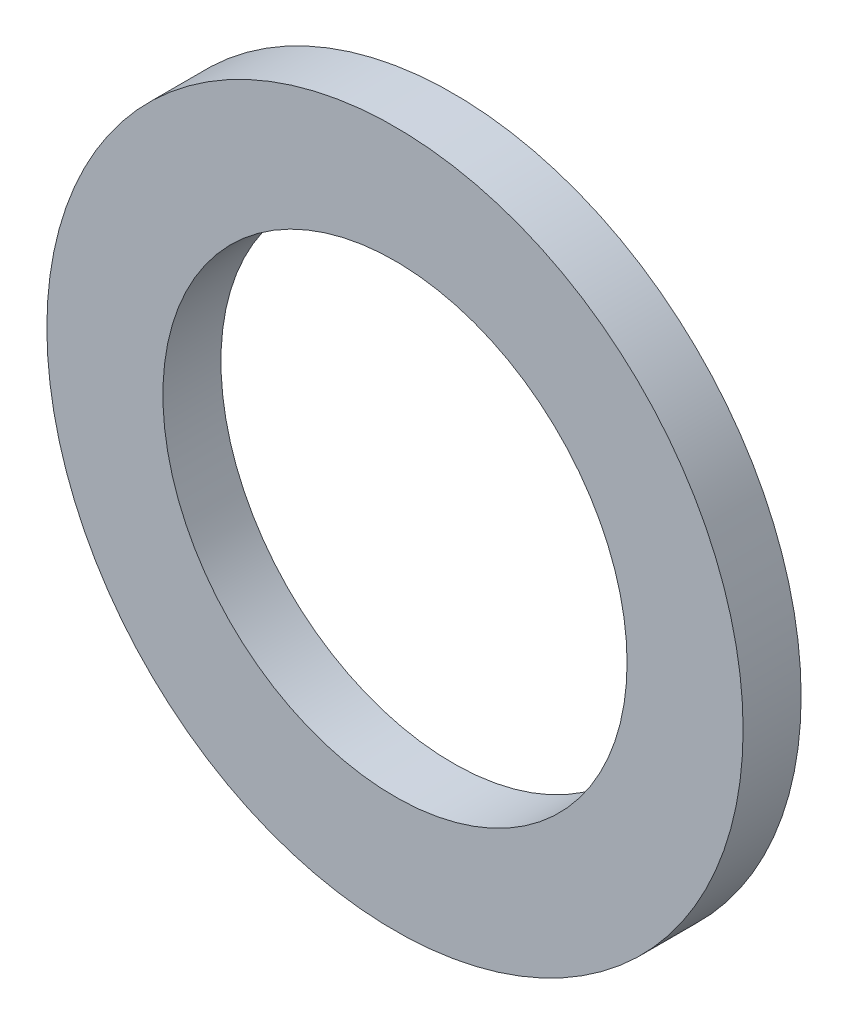
SolidWorks part; units mm, degrees
ref_plane "Plan de face" through (0, 0, 0) normal (0, 0, 1) x (1, 0, 0)
ref_plane "Plan de dessus" through (0, 0, 0) normal (0, 1, 0) x (1, 0, 0)
ref_plane "Plan de droite" through (0, 0, 0) normal (1, 0, 0) x (0, 0, -1)
sketch "Esquisse1" plane through (0, 0, 0) normal (0, 0, 1) x (1, 0, 0)
  circle A0 centre (0, 0) radius 4
  circle A1 centre (0, 0) radius 6
extrude "Extrusion1" add sketch "Esquisse1" along normal blind 1
